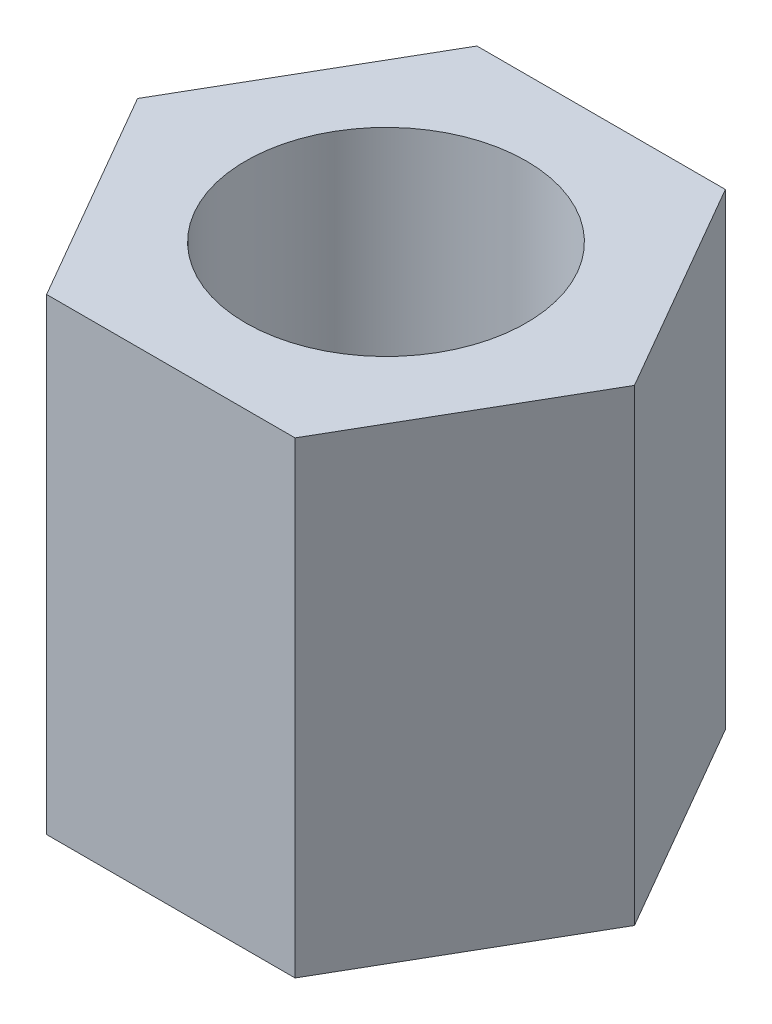
SolidWorks part; units mm, degrees
ref_plane "前视基准面" through (0, 0, 0) normal (0, 0, 1) x (1, 0, 0)
ref_plane "上视基准面" through (0, 0, 0) normal (0, 1, 0) x (1, 0, 0)
ref_plane "右视基准面" through (0, 0, 0) normal (1, 0, 0) x (0, 0, -1)
sketch "草图1" plane through (0, 0, 0) normal (0, 1, 0) x (1, 0, 0)
  line L1 (-1.3279, 2.3) -> (-2.6558, 0)
  line L2 (-2.6558, 0) -> (-1.3279, -2.3)
  line L3 (-1.3279, -2.3) -> (1.3279, -2.3)
  line L4 (1.3279, -2.3) -> (2.6558, 0)
  line L5 (2.6558, 0) -> (1.3279, 2.3)
  line L6 (1.3279, 2.3) -> (-1.3279, 2.3)
  circle A0 centre (0, 0) radius 2.3
  circle A1 centre (0, 0) radius 2.3 construction
  circle A2 centre (0, 0) radius 1.5
  dimension "D1" = 4.6
  dimension "D4" = 3
  dimension "D2" = 4.6
  dimension "D3" = 5.3116
extrude "凸台-拉伸2" add sketch "草图1" along normal blind 5 contours A0 A2 | A0 L6 L1 | A0 L1 L2 | A0 L5 L6 | A0 L4 L5 | A0 L3 L4 | A0 L2 L3
